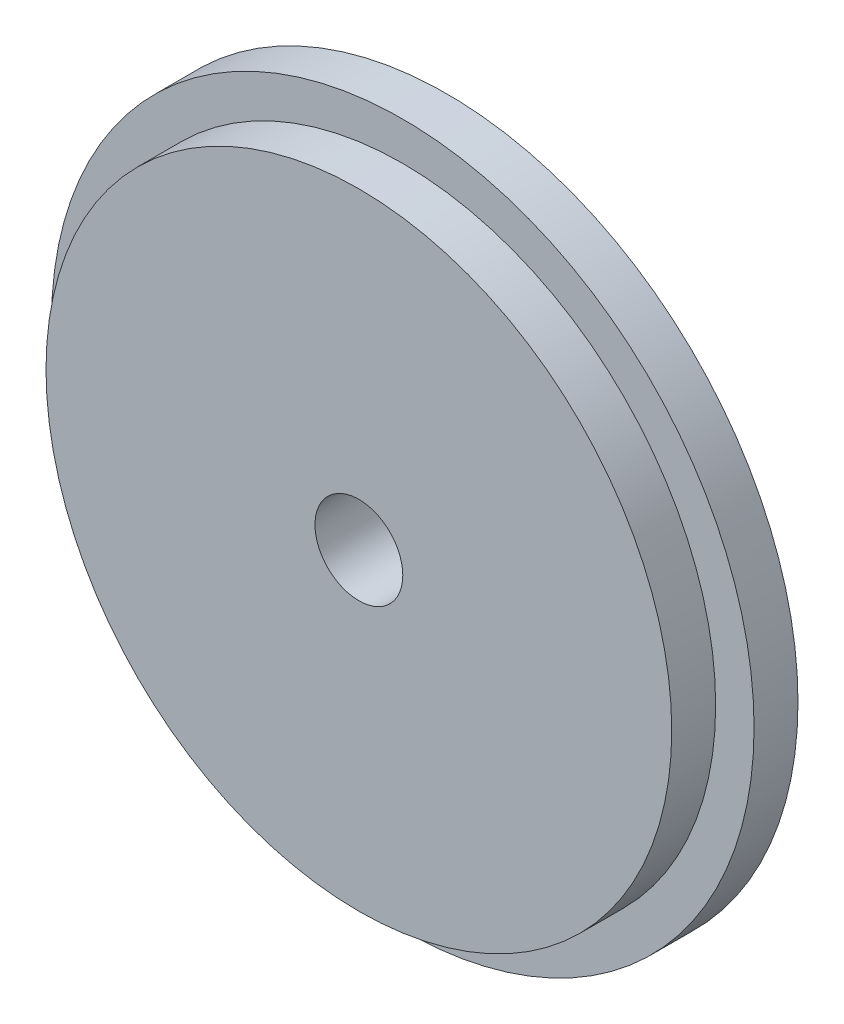
SolidWorks part; units mm, degrees
ref_plane "Plan de face" through (0, 0, 0) normal (0, 0, 1) x (1, 0, 0)
ref_plane "Plan de dessus" through (0, 0, 0) normal (0, 1, 0) x (1, 0, 0)
ref_plane "Plan de droite" through (0, 0, 0) normal (1, 0, 0) x (0, 0, -1)
sketch "Esquisse1" plane through (0, 0, 0) normal (0, 0, 1) x (1, 0, 0)
  circle A0 centre (0, 0) radius 16
  dimension "D1" = 32
extrude "Boss.-Extru.1" add sketch "Esquisse1" along normal blind 2
sketch "Esquisse2" plane through (0, 0, 2) normal (0, 0, 1) x (1, 0, 0)
  circle A0 centre (0, 0) radius 14.25
  dimension "D1" = 28.5
extrude "Boss.-Extru.2" add sketch "Esquisse2" along normal blind 2
sketch "Esquisse3" plane through (0, 0, 4) normal (0, 0, 1) x (1, 0, 0)
  circle A0 centre (0, 0) radius 2
  dimension "D1" = 4
extrude "Enlèv. mat.-Extru.1" cut sketch "Esquisse3" against normal through all
